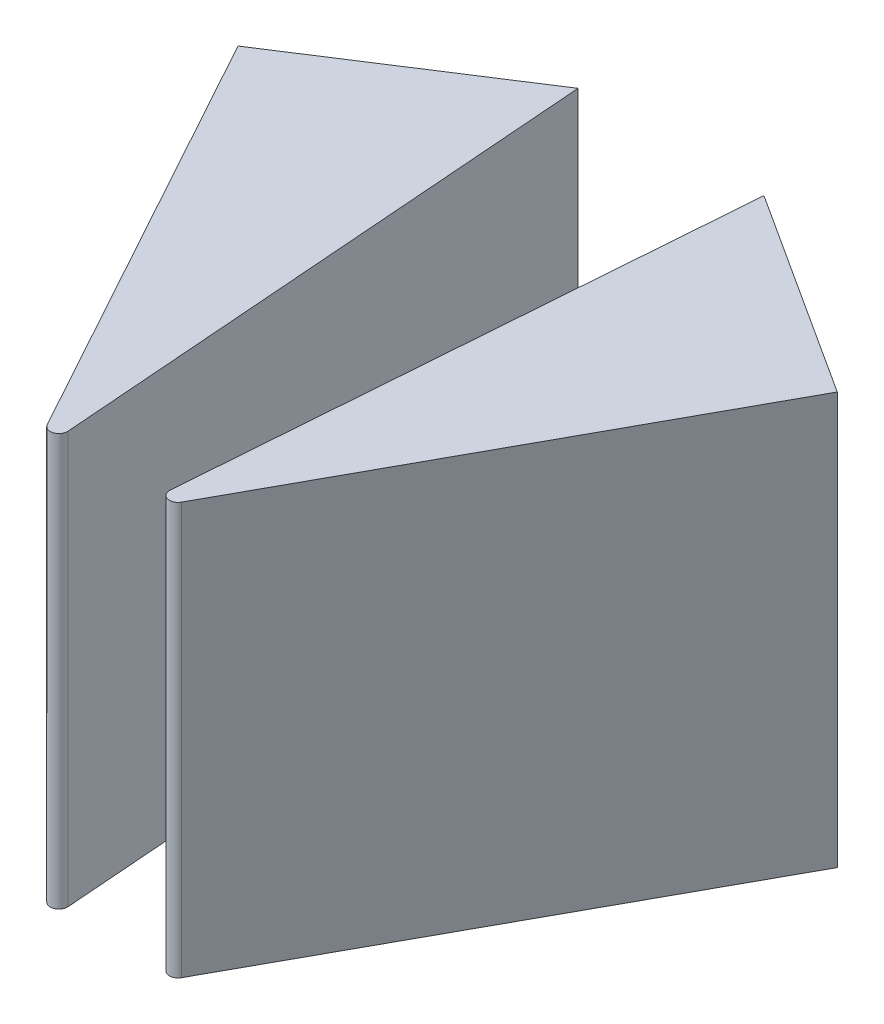
SolidWorks part; units mm, degrees
ref_plane "Front Plane" through (0, 0, 0) normal (0, 0, 1) x (1, 0, 0)
ref_plane "Top Plane" through (0, 0, 0) normal (0, 1, 0) x (1, 0, 0)
ref_plane "Right Plane" through (0, 0, 0) normal (1, 0, 0) x (0, 0, -1)
sketch "Sketch1" plane through (0, 0, 0) normal (0, 1, 0) x (1, 0, 0)
  line L0 (0, -82.5235) -> (0, 103.8309) construction
  line L1 (0, 12.3614) -> (43.6478, -15.8065) construction
  line L2 (43.6478, -15.8065) -> (7, -82.5235) construction
  line L3 (7, -82.5235) -> (7, 7.844) construction
  line L4 (7, -82.5235) -> (0, -82.5235) construction
  line L5 (7, -82.5235) -> (13.5406, 3.623) construction
  dimension "D1" = 7
sketch "Sketch2" plane through (0, 0, 0) normal (0, 1, 0) x (1, 0, 0)
  line L0 (13.5406, 3.623) -> (7.437, -76.7679)
  line L1 (13.5406, 3.623) -> (43.6478, -15.8065)
  line L2 (43.6478, -15.8065) -> (9.779, -77.4644)
  arc A0 (7.437, -76.7679) -> (9.779, -77.4644) centre (8.6834, -76.8626) ccw
  point P8 (7, -82.5235)
  dimension "D1" = 1.25
extrude "Boss-Extrude1" add sketch "Sketch2" along normal blind 60
mirror "Mirror2" about plane through (0, 0, 0) normal (1, 0, 0) of bodies 101
